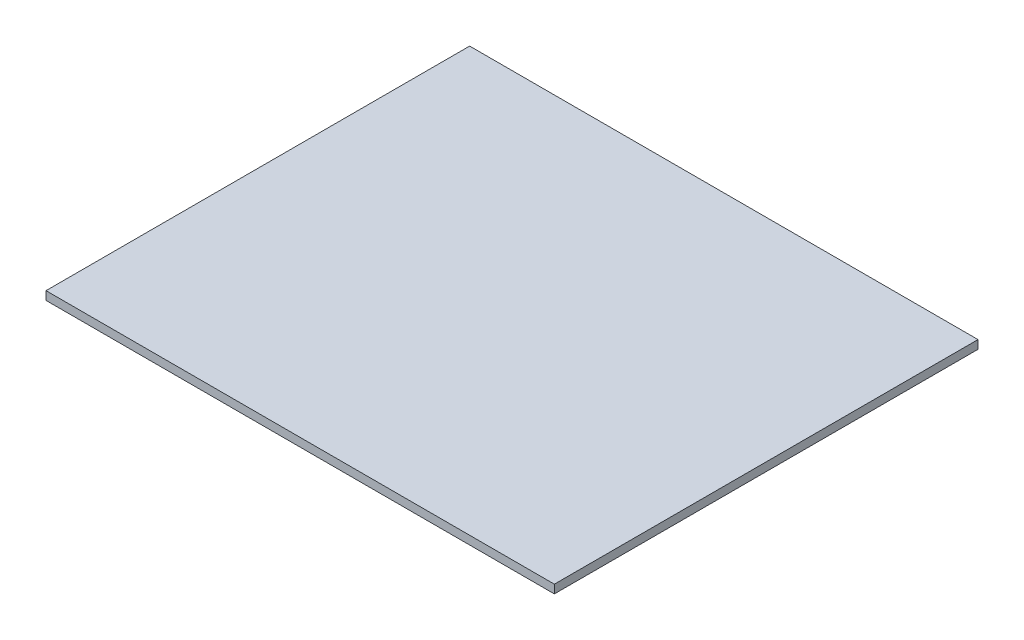
SolidWorks part; units mm, degrees
ref_plane "Front Plane" through (0, 0, 0) normal (0, 0, 1) x (1, 0, 0)
ref_plane "Top Plane" through (0, 0, 0) normal (0, 1, 0) x (1, 0, 0)
ref_plane "Right Plane" through (0, 0, 0) normal (1, 0, 0) x (0, 0, -1)
sketch "Sketch1" plane through (0, 0, 0) normal (0, 1, 0) x (1, 0, 0)
  line L1 (-0.6, 0.5) -> (0.6, 0.5)
  line L2 (-0.6, 0.5) -> (-0.6, -0.5)
  line L3 (-0.6, -0.5) -> (0.6, -0.5)
  line L4 (0.6, 0.5) -> (0.6, -0.5)
  point P4 (0, 0)
  point P5 (0, 0)
  point P6 (0, 0)
  point P7 (0, 0)
  point P8 (0, 0)
  point P9 (0, 0)
  point P10 (0, 0)
extrude "Boss-Extrude1" add sketch "Sketch1" along normal blind 0.02 contours L1 L4 L3 L2
